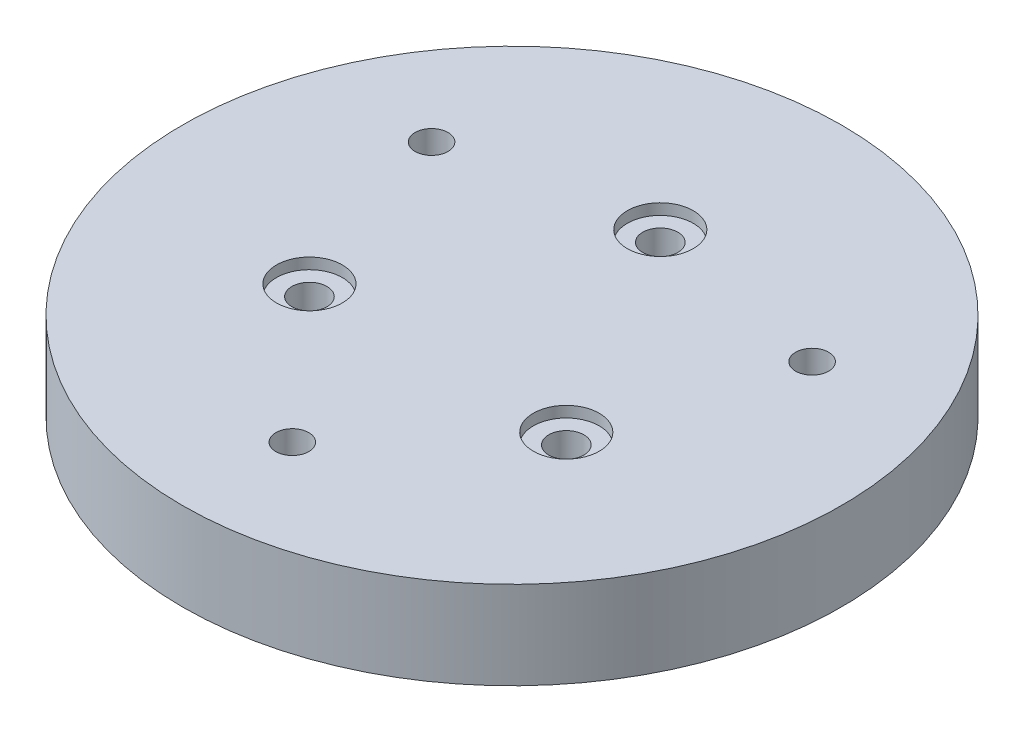
SolidWorks part; units mm, degrees
ref_plane "前视基准面" through (0, 0, 0) normal (0, 0, 1) x (1, 0, 0)
ref_plane "上视基准面" through (0, 0, 0) normal (0, 1, 0) x (1, 0, 0)
ref_plane "右视基准面" through (0, 0, 0) normal (1, 0, 0) x (0, 0, -1)
sketch "草图1" plane through (0, 0, 0) normal (0, 1, 0) x (1, 0, 0)
  circle A0 centre (0, 0) radius 30
extrude "凸台-拉伸1" add sketch "草图1" along normal blind 8
sketch "草图2" plane through (0, 8, 0) normal (0, 1, 0) x (1, 0, 0)
  circle A0 centre (0, 0) radius 13.5
  circle A1 centre (0, 13.5) radius 1.6
  circle A2 centre (11.6913, -6.75) radius 1.6
  circle A3 centre (-11.6913, -6.75) radius 1.6
  point P11 (0, 0)
  dimension "D1" = 3
extrude "切除-拉伸1" cut sketch "草图2" against normal blind 15 contours A1 | A3 | A2
sketch "草图3" plane through (0, 8, 0) normal (0, 1, 0) x (1, 0, 0)
  line L0 (0, 0) -> (17.3205, 10)
  circle A0 centre (0, 0) radius 20
  circle A1 centre (17.3205, 10) radius 1.5
  circle A2 centre (0, -20) radius 1.5
  circle A3 centre (-17.3205, 10) radius 1.5
  point P5 (0, 0)
  point P6 (0, 0)
  point P11 (0, 0)
  point P13 (0, 20)
  point P14 (0, 0)
  point P15 (17.5938, 10.6972)
  dimension "D1" = 3
extrude "切除-拉伸2" cut sketch "草图3" against normal blind 8 contours A1 | A3 | A2
sketch "草图4" plane through (0, 8, 0) normal (0, 1, 0) x (1, 0, 0)
  circle A0 centre (0, 13.5) radius 3
  circle A1 centre (11.6913, -6.75) radius 3
  circle A2 centre (-11.6913, -6.75) radius 3
  point P9 (0, 0)
  dimension "D1" = 3
extrude "切除-拉伸3" cut sketch "草图4" against normal blind 1
sketch "草图5" plane through (0, 0, 0) normal (0, -1, 0) x (1, 0, 0)
  line L0 (16.0215, -12.25) -> (18.6195, -12.25)
  line L1 (2.5981, 20) -> (1.299, 22.25)
  line L2 (1.299, 22.25) -> (-1.299, 22.25)
  line L3 (-1.299, 22.25) -> (-2.5981, 20)
  line L4 (-2.5981, 20) -> (-1.299, 17.75)
  line L5 (-1.299, 17.75) -> (1.299, 17.75)
  line L6 (1.299, 17.75) -> (2.5981, 20)
  line L7 (18.6195, -12.25) -> (19.9186, -10)
  line L8 (19.9186, -10) -> (18.6195, -7.75)
  line L9 (18.6195, -7.75) -> (16.0215, -7.75)
  line L10 (16.0215, -7.75) -> (14.7224, -10)
  line L11 (14.7224, -10) -> (16.0215, -12.25)
  line L12 (-18.6195, -7.75) -> (-19.9186, -10)
  line L13 (-19.9186, -10) -> (-18.6195, -12.25)
  line L14 (-18.6195, -12.25) -> (-16.0215, -12.25)
  line L15 (-16.0215, -12.25) -> (-14.7224, -10)
  line L16 (-14.7224, -10) -> (-16.0215, -7.75)
  line L17 (-16.0215, -7.75) -> (-18.6195, -7.75)
  circle A0 centre (0, 20) radius 2.25 construction
  point P24 (0, 0)
  circle M7 centre (17.3205, -10) radius 1.5
  circle M8 centre (-17.3205, -10) radius 1.5
  dimension "D1" = 3
extrude "切除-拉伸4" cut sketch "草图5" against normal blind 4 contours L16 L17 L12 L13 L14 L15 M8 | L10 L11 L0 L7 L8 L9 M7 | L2 L3 L4 L5 L6 L1
